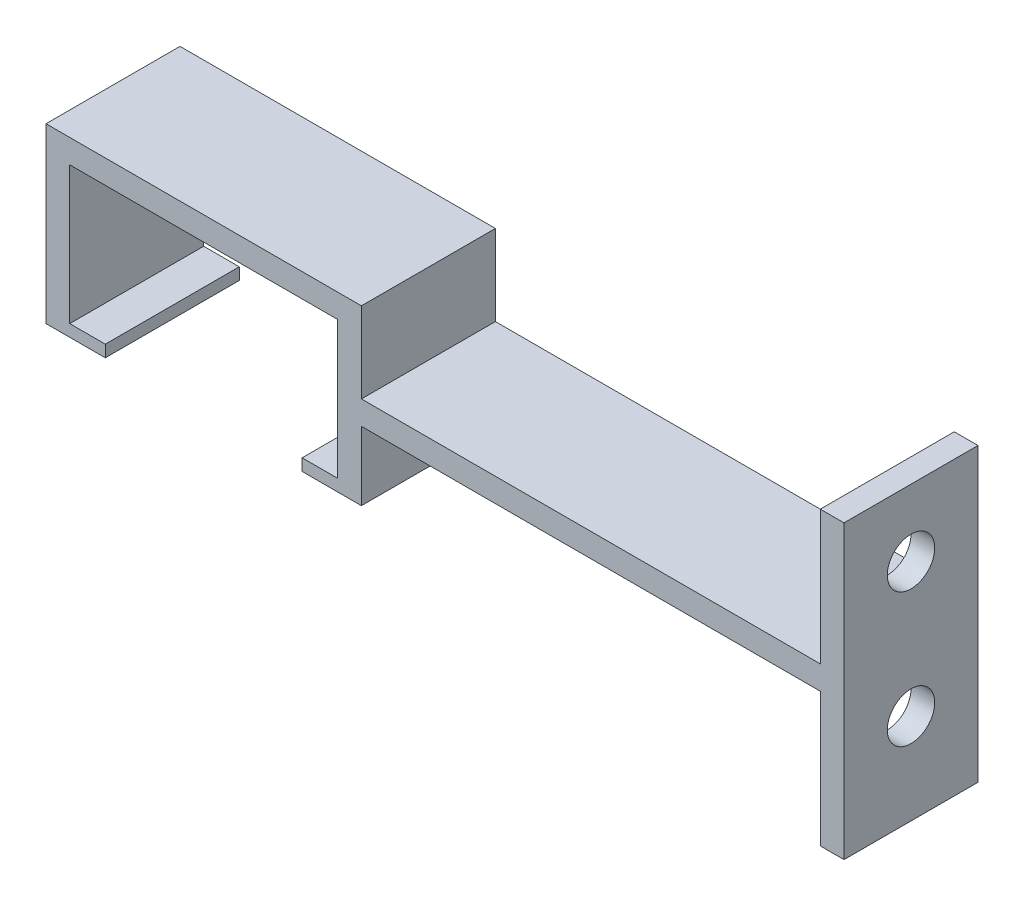
SolidWorks part; units mm, degrees
ref_plane "Plan de face" through (0, 0, 0) normal (0, 0, 1) x (1, 0, 0)
ref_plane "Plan de dessus" through (0, 0, 0) normal (0, 1, 0) x (1, 0, 0)
ref_plane "Plan de droite" through (0, 0, 0) normal (1, 0, 0) x (0, 0, -1)
sketch "Esquisse1" plane through (0, 0, 0) normal (0, 0, 1) x (1, 0, 0)
  line L0 (-20.6, 1) -> (-20.6, 0)
  line L1 (0, 0) -> (-4, 0)
  line L2 (0, 0) -> (0, 13.6)
  line L3 (0, 13.6) -> (-24.6, 13.6)
  line L4 (-24.6, 0) -> (-24.6, 13.6)
  line L5 (-23.6, 12.6) -> (-1, 12.6)
  line L6 (-23.6, 12.6) -> (-23.6, 1)
  line L7 (-23.6, 1) -> (-20.6, 1)
  line L8 (-1, 12.6) -> (-1, 1)
  line L9 (-4, 1) -> (-4, 0)
  line L10 (-4, 1) -> (-1, 1)
  line L11 (-20.6, 0) -> (-24.6, 0)
  dimension "D1" = 13.6
  dimension "D2" = 24.6
  dimension "D3" = 1
  dimension "D4" = 1
  dimension "D5" = 1
  dimension "D6" = 1
  dimension "D7" = 4
  dimension "D8" = 4
extrude "Boss.-Extru.1" add sketch "Esquisse1" along normal blind 11.3
sketch "Esquisse2" plane through (0, 13.6, 0) normal (0, 1, 0) x (1, 0, 0)
  line L0 (0, -11.3) -> (-24.6, -11.3) construction
  line L1 (-16.6, 0) -> (-8, 0)
  line L2 (-16.6, 0) -> (-16.6, -11.3)
  line L3 (-16.6, -11.3) -> (-8, -11.3)
  line L4 (-8, 0) -> (-8, -11.3)
  line L5 (-24.6, -11.3) -> (-24.6, 0) construction
  line L6 (0, -11.3) -> (0, 0) construction
  dimension "D1" = 8
  dimension "D2" = 8
  dimension "D3" = 11.3
extrude "Boss.-Extru.2" add sketch "Esquisse2" along normal blind 1
sketch "Esquisse8" plane through (-8, 0, 0) normal (1, 0, 0) x (0, 0, -1)
  line L1 (-11.3, 13.6) -> (0, 13.6)
  line L2 (-11.3, 13.6) -> (-11.3, 14.6)
  line L3 (-11.3, 14.6) -> (0, 14.6)
  line L4 (0, 13.6) -> (0, 14.6)
  dimension "D1" = 11.3
extrude "Boss.-Extru.5" add sketch "Esquisse8" along normal blind 10
sketch "Esquisse9" plane through (0, 13.6, 0) normal (0, -1, 0) x (1, 0, 0)
  line L1 (2, 11.3) -> (0, 11.3)
  line L2 (2, 11.3) -> (2, 0)
  line L3 (2, 0) -> (0, 0)
  line L4 (0, 11.3) -> (0, 0)
extrude "Boss.-Extru.6" add sketch "Esquisse9" along normal blind 7.8
sketch "Esquisse10" plane through (2, 0, 0) normal (1, 0, 0) x (0, 0, -1)
  line L0 (0, 5.8) -> (0, 0) construction
  line L1 (-11.3, 5.8) -> (0, 5.8)
  line L2 (-11.3, 5.8) -> (-11.3, 7.8)
  line L3 (-11.3, 7.8) -> (0, 7.8)
  line L4 (0, 5.8) -> (0, 7.8)
  dimension "D1" = 2
extrude "Boss.-Extru.7" add sketch "Esquisse10" along normal blind 39.7
sketch "Esquisse11" plane through (0, 5.8, 0) normal (0, -1, 0) x (1, 0, 0)
  line L0 (41.7, 11.3) -> (0, 11.3) construction
  line L1 (41.7, 0) -> (39.7, 0)
  line L2 (41.7, 0) -> (41.7, 11.3)
  line L3 (41.7, 11.3) -> (39.7, 11.3)
  line L4 (39.7, 0) -> (39.7, 11.3)
  dimension "D1" = 2
extrude "Boss.-Extru.8" add sketch "Esquisse11" along normal blind 11.3
sketch "Esquisse12" plane through (0, 7.8, 0) normal (0, 1, 0) x (1, 0, 0)
  line L0 (41.7, 0) -> (2, 0) construction
  line L1 (41.7, -11.3) -> (39.7, -11.3)
  line L2 (41.7, -11.3) -> (41.7, 0)
  line L3 (41.7, 0) -> (39.7, 0)
  line L4 (39.7, -11.3) -> (39.7, 0)
  dimension "D1" = 2
extrude "Boss.-Extru.9" add sketch "Esquisse12" along normal blind 11.3
sketch "Esquisse13" plane through (0, 0, 11.3) normal (0, 0, 1) x (1, 0, 0)
  line L0 (-16.6, 14.6) -> (-25.6, 14.6)
  line L1 (-25.6, 14.6) -> (-25.6, 0)
  line L2 (-25.6, 0) -> (-24.6, 0)
  line L3 (-24.6, 13.6) -> (-24.6, 0) construction
  line L4 (-16.6, 13.6) -> (-24.6, 13.6) construction
  line L6 (-24.6, 0) -> (-24.6, 13.6)
  line L7 (-24.6, 13.6) -> (-16.6, 13.6)
  line L8 (-16.6, 13.6) -> (-16.6, 14.6)
  dimension "D1" = 1
  dimension "D2" = 1
extrude "Boss.-Extru.10" add sketch "Esquisse13" against normal up to vertex (11.3 mm away)
sketch "Esquisse14" plane through (0, 5.8, 0) normal (0, -1, 0) x (1, 0, 0)
  line L0 (0, 11.3) -> (1, 11.3)
  line L1 (39.7, 11.3) -> (0, 11.3) construction
  line L2 (1, 11.3) -> (1, 0)
  line L3 (0, 0) -> (39.7, 0) construction
  line L4 (1, 0) -> (0, 0)
  line L5 (0, 0) -> (0, 11.3)
  dimension "D1" = 1
extrude "Boss.-Extru.11" add sketch "Esquisse14" along normal up to vertex
sketch "Esquisse16" plane through (2, 0, 0) normal (1, 0, 0) x (0, 0, -1)
  line L0 (-11.3, 14.6) -> (0, 14.6)
  line L1 (0, 14.6) -> (0, 7.8)
  line L2 (0, 7.8) -> (-11.3, 7.8)
  line L3 (-11.3, 7.8) -> (-11.3, 14.6)
extrude "Enlèv. mat.-Extru.1" cut sketch "Esquisse16" against normal blind 1
sketch "Esquisse19" plane through (41.7, 0, 0) normal (1, 0, 0) x (0, 0, -1)
  line L0 (-11.3, 7.8) -> (0, 7.8) construction
  line L1 (-11.3, 19.1) -> (-11.3, -5.5) construction
  line L2 (-11.3, 19.1) -> (0, 19.1) construction
  circle A0 centre (-5.65, 13.45) radius 2
  circle A1 centre (-5.65, 2.15) radius 2
  dimension "D1" = 4
  dimension "D2" = 5.65
  dimension "D3" = 5.65
extrude "Enlèv. mat.-Extru.3" cut sketch "Esquisse19" against normal blind 10
